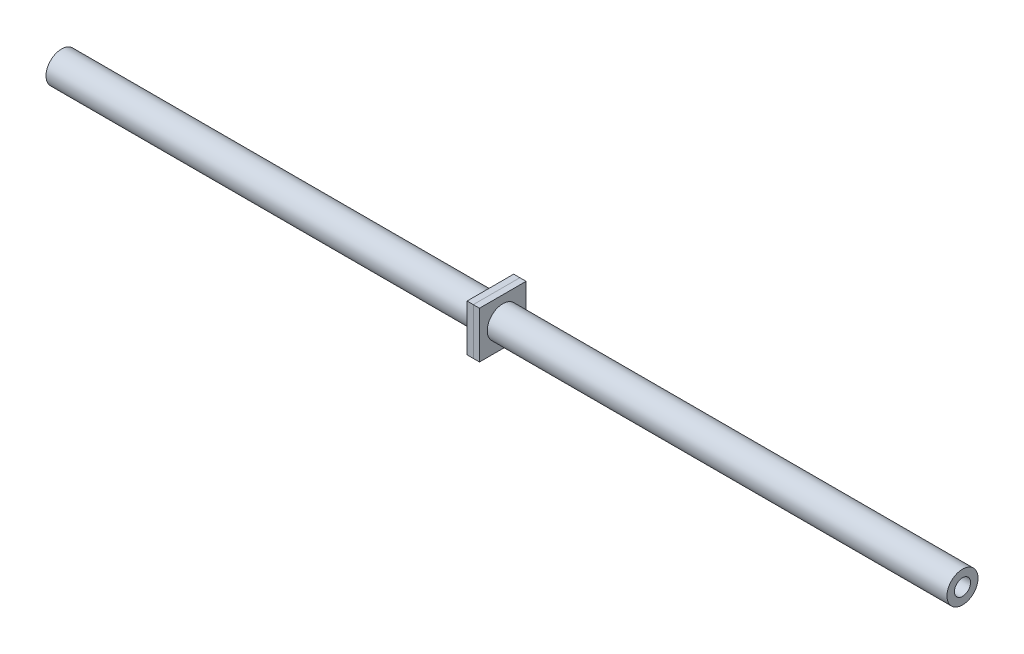
SolidWorks part; units mm, degrees
material "AISI 4130 Steel, normalized at 870C"
ref_plane "Front Plane" through (0, 0, 0) normal (0, 0, 1) x (1, 0, 0)
ref_plane "Top Plane" through (0, 0, 0) normal (0, 1, 0) x (1, 0, 0)
ref_plane "Right Plane" through (0, 0, 0) normal (1, 0, 0) x (0, 0, -1)
sketch "Pull Rod" plane through (0, 0, 0) normal (0, 0, 1) x (1, 0, 0)
  line L0 (0, 0) -> (368.2148, 0)
  line L1 (0, 0) -> (-27.8003, 0) construction
  line L2 (368.2148, 0) -> (396.0151, 0) construction
  dimension "D1" = 27.8003
  dimension "D2" = 423.8154
other "Pull Rod Member"
ref_plane "Plane1" through (0, 0, 0) normal (1, 0, 0) x (0, 1, 0)
sketch "Sketch11" plane through (0, 0, 0) normal (1, 0, 0) x (0, 1, 0)
  circle A0 centre (0, 0) radius 6.35
  circle A1 centre (0, 0) radius 3.302
  point P3 (0, 0)
  dimension "D1" = 12.7
  dimension "D2" = 3.048
sketch "Sketch12" plane through (0, 0, 0) normal (1, 0, 0) x (0, 0, -1)
  line L1 (9.525, 9.525) -> (-9.525, 9.525)
  line L2 (9.525, 9.525) -> (9.525, -9.525)
  line L3 (9.525, -9.525) -> (-9.525, -9.525)
  line L4 (-9.525, 9.525) -> (-9.525, -9.525)
  line L5 (9.525, 9.525) -> (-9.525, -9.525) construction
  line L6 (9.525, -9.525) -> (-9.525, 9.525) construction
  circle A0 centre (0, 0) radius 6.35 construction
  circle A1 centre (0, 0) radius 6.35
  point P0 (0, 0)
  dimension "D1" = 19.05
extrude "Pull Rod Nut 1" add sketch "Sketch12" along normal blind 2.54 from offset 177.8 separate body
sketch "Sketch13" plane through (0, 0, 0) normal (1, 0, 0) x (0, 0, -1)
  line L0 (9.525, 9.525) -> (-9.525, 9.525) construction
  line L1 (9.525, -9.525) -> (-9.525, -9.525) construction
  line L2 (9.525, 9.525) -> (9.525, -9.525) construction
  line L3 (-9.525, 9.525) -> (-9.525, -9.525) construction
  line L4 (9.525, 9.525) -> (-9.525, 9.525)
  line L5 (9.525, -9.525) -> (-9.525, -9.525)
  line L6 (9.525, 9.525) -> (9.525, -9.525)
  line L7 (-9.525, 9.525) -> (-9.525, -9.525)
  circle A0 centre (0, 0) radius 6.35 construction
  circle A1 centre (0, 0) radius 6.35
extrude "Pull Rod Nut 2" add sketch "Sketch13" against normal blind 2.54 from surface at 177.8 separate body starting at face at (177.8, 0, 0)
